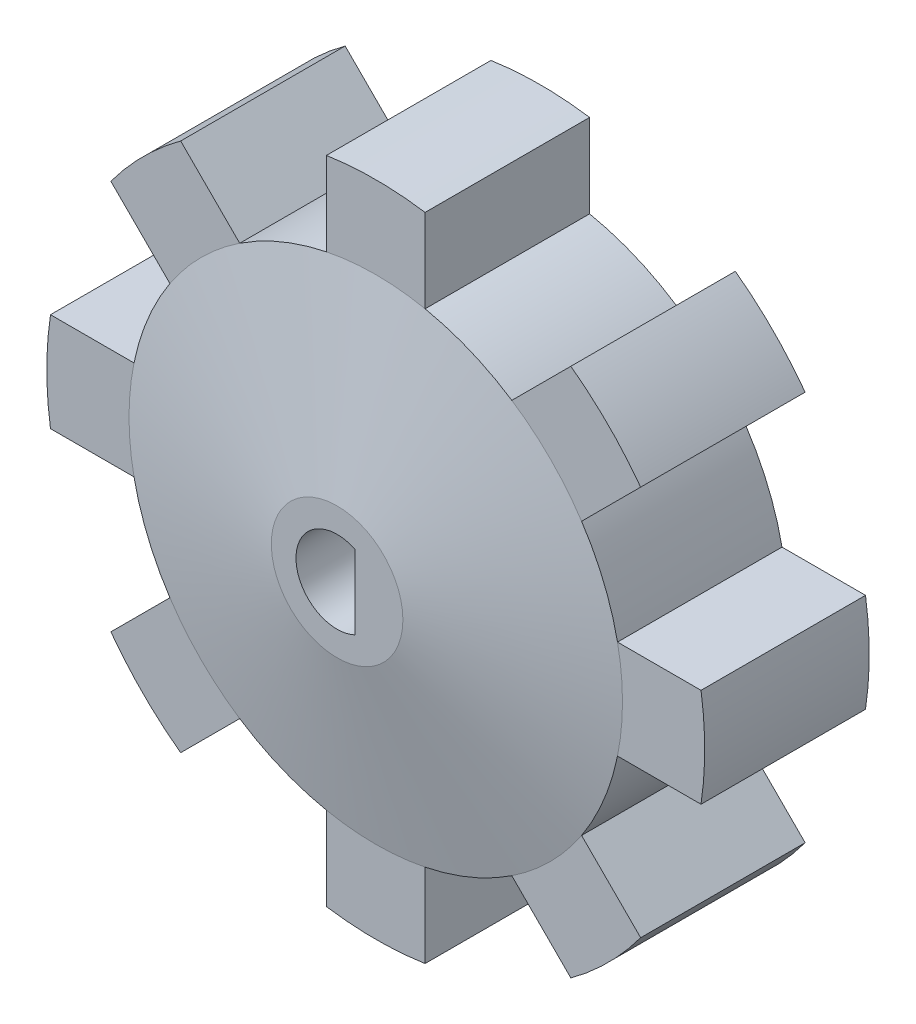
SolidWorks part; units mm, degrees
ref_plane "Front Plane" through (0, 0, 0) normal (0, 0, 1) x (1, 0, 0)
ref_plane "Top Plane" through (0, 0, 0) normal (0, 1, 0) x (1, 0, 0)
ref_plane "Right Plane" through (0, 0, 0) normal (1, 0, 0) x (0, 0, -1)
sketch "Sketch3" plane through (0, 0, 0) normal (1, 0, 0) x (0, 0, -1)
  line L0 (0, 0) -> (14.7, 0)
  line L4 (2.35, 15) -> (2.35, 20)
  line L5 (2.35, 20) -> (12.35, 20)
  line L6 (12.35, 20) -> (12.35, 15)
  line L8 (0, 4) -> (0, 0)
  line L9 (14.7, 4) -> (14.7, 0)
  line L10 (2.35, 15) -> (0, 4)
  line L11 (12.35, 15) -> (14.7, 4)
  dimension "D1" = 14.7
  dimension "D2" = 5
  dimension "D3" = 10
  dimension "D4" = 20
  dimension "D5" = 4
revolve "Revolve3" add sketch "Sketch3" angle 360 about L0
sketch "Sketch2" plane through (0, 0, 0) normal (0, 0, 1) x (1, 0, 0)
  line L1 (3, 14.6969) -> (3, 19.7737)
  line L2 (3, 19.7737) -> (-3, 19.7737)
  line L3 (-3, 19.7737) -> (-3, 14.6969)
  line L4 (11.8608, 16.1035) -> (8.271, 12.5136)
  line L5 (16.1035, 11.8608) -> (11.8608, 16.1035)
  line L6 (12.5136, 8.271) -> (16.1035, 11.8608)
  line L7 (19.7737, 3) -> (14.6969, 3)
  line L8 (19.7737, -3) -> (19.7737, 3)
  line L9 (14.6969, -3) -> (19.7737, -3)
  line L10 (16.1035, -11.8608) -> (12.5136, -8.271)
  line L11 (11.8608, -16.1035) -> (16.1035, -11.8608)
  line L12 (8.271, -12.5136) -> (11.8608, -16.1035)
  line L13 (3, -19.7737) -> (3, -14.6969)
  line L14 (-3, -19.7737) -> (3, -19.7737)
  line L15 (-3, -14.6969) -> (-3, -19.7737)
  line L16 (-11.8608, -16.1035) -> (-8.271, -12.5136)
  line L17 (-16.1035, -11.8608) -> (-11.8608, -16.1035)
  line L18 (-12.5136, -8.271) -> (-16.1035, -11.8608)
  line L19 (-19.7737, -3) -> (-14.6969, -3)
  line L20 (-19.7737, 3) -> (-19.7737, -3)
  line L21 (-14.6969, 3) -> (-19.7737, 3)
  line L22 (-16.1035, 11.8608) -> (-12.5136, 8.271)
  line L23 (-11.8608, 16.1035) -> (-16.1035, 11.8608)
  line L24 (-8.271, 12.5136) -> (-11.8608, 16.1035)
  circle A0 centre (0, 0) radius 20
  circle A1 centre (0, 0) radius 15
  circle A2 centre (0, 0) radius 25
  circle A3 centre (0, 0) radius 2.5
  point P39 (0, 0)
  dimension "D1" = 40
  dimension "D2" = 30
  dimension "D5" = 50
  dimension "D6" = 5
  dimension "D3" = 6
  dimension "D4" = 8
extrude "Cut-Extrude5" cut sketch "Sketch2" against normal blind 30 contours A2 A0 | A1 L19 A0 L18 | A1 L22 A0 L21 | A1 L3 A0 L24 | A1 L4 A0 L1 | A1 L7 A0 L6 | A1 L10 A0 L9 | A1 L13 A0 L12 | A1 L16 A0 L15
sketch "Sketch4" plane through (0, 0, 0) normal (0, 0, 1) x (1, 0, 0)
  line L0 (1.0897, 2.25) -> (1.0897, -2.25)
  circle A0 centre (0, 0) radius 2.5
  point P0 (0, 0)
  dimension "D1" = 5
  dimension "D2" = 4.5
extrude "Cut-Extrude6" cut sketch "Sketch4" against normal blind 20 contours L0 A0
